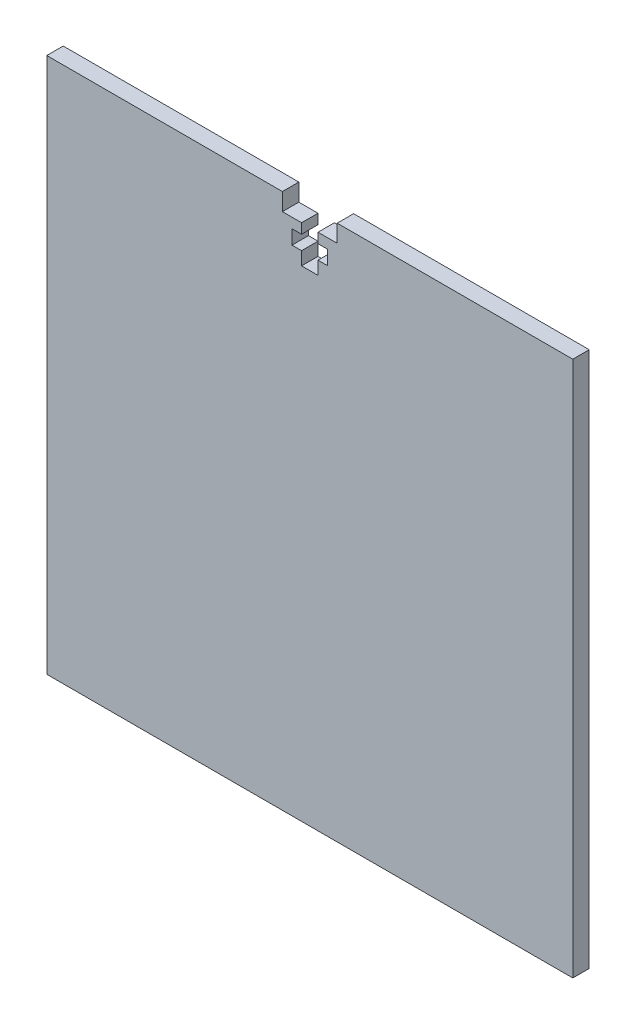
SolidWorks part; units mm, degrees
ref_plane "Front Plane" through (0, 0, 0) normal (0, 0, 1) x (1, 0, 0)
ref_plane "Top Plane" through (0, 0, 0) normal (0, 1, 0) x (1, 0, 0)
ref_plane "Right Plane" through (0, 0, 0) normal (1, 0, 0) x (0, 0, -1)
sketch "Sketch1" plane through (0, 0, 0) normal (0, 0, 1) x (1, 0, 0)
  line L1 (-47.9962, 48.8994) -> (47.9962, 48.8994)
  line L2 (-47.9962, 48.8994) -> (-47.9962, -48.8994)
  line L3 (-47.9962, -48.8994) -> (47.9962, -48.8994)
  line L4 (47.9962, 48.8994) -> (47.9962, -48.8994)
  line L5 (-47.9962, 48.8994) -> (47.9962, -48.8994) construction
  line L6 (-47.9962, -48.8994) -> (47.9962, 48.8994) construction
  point P0 (0, 0)
extrude "Boss-Extrude1" add sketch "Sketch1" along normal blind 3
sketch "Sketch2" plane through (0, 0, 3) normal (0, 0, 1) x (1, 0, 0)
  line L0 (0, 48.8994) -> (0, 38.8994) construction
  line L1 (47.9962, 48.8994) -> (-47.9962, 48.8994) construction
  line L2 (1.5, 45.7194) -> (5, 45.7194)
  line L3 (-5, 48.8994) -> (5, 48.8994)
  line L4 (-5, 48.8994) -> (-5, 45.7194)
  line L5 (-5, 45.7194) -> (-1.5, 45.7194)
  line L6 (5, 48.8994) -> (5, 45.7194)
  line L8 (-1.5, 45.7194) -> (-1.5, 43.8994)
  line L9 (-1.5, 38.8994) -> (1.5, 38.8994)
  line L10 (1.5, 45.7194) -> (1.5, 43.8994)
  line L11 (-3.25, 43.8994) -> (3.25, 43.8994) construction
  line L12 (-3.25, 43.8994) -> (-3.25, 41.2994)
  line L13 (-3.25, 41.2994) -> (-1.5, 41.2994)
  line L14 (3.25, 43.8994) -> (3.25, 41.2994)
  line L15 (-1.5, 41.2994) -> (-1.5, 38.8994)
  line L16 (1.5, 41.2994) -> (3.25, 41.2994)
  line L17 (1.5, 41.2994) -> (1.5, 38.8994)
  line L18 (-3.25, 43.8994) -> (-1.5, 43.8994)
  line L19 (3.25, 43.8994) -> (1.5, 43.8994)
  point P17 (0, 43.8994)
  dimension "D1" = 3.18
  dimension "D2" = 10
  dimension "D3" = 3
  dimension "D4" = 2.6
  dimension "D5" = 6.5
  dimension "D6" = 10
extrude "Cut-Extrude1" cut sketch "Sketch2" against normal through all
